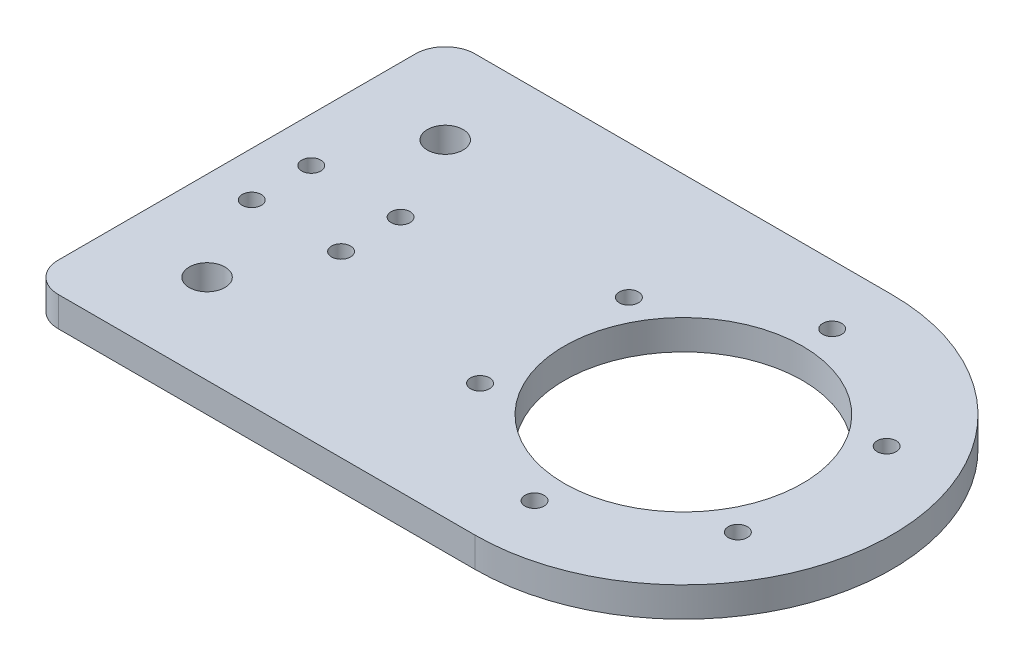
SolidWorks part; units mm, degrees
ref_plane "Front Plane" through (0, 0, 0) normal (0, 0, 1) x (1, 0, 0)
ref_plane "Top Plane" through (0, 0, 0) normal (0, 1, 0) x (1, 0, 0)
ref_plane "Right Plane" through (0, 0, 0) normal (1, 0, 0) x (0, 0, -1)
sketch "Sketch1" plane through (0, 0, 0) normal (0, 1, 0) x (1, 0, 0)
  line L0 (-75, 35) -> (0, 35)
  line L1 (0, -35) -> (-75, -35)
  line L2 (-75, -35) -> (-75, 35)
  line L3 (-60, 20) -> (-60, -20) construction
  line L4 (-103.0809, 0) -> (63.3859, 0) construction
  line L5 (-67.5, 5) -> (-52.5, 5) construction
  line L6 (-67.5, 5) -> (-67.5, -5) construction
  line L7 (-67.5, -5) -> (-52.5, -5) construction
  line L8 (-52.5, 5) -> (-52.5, -5) construction
  line L9 (-67.5, 5) -> (-52.5, -5) construction
  line L10 (-67.5, -5) -> (-52.5, 5) construction
  circle A0 centre (0, 0) radius 25 construction
  circle A1 centre (0, 25) radius 1.6
  arc A2 (0, 35) -> (0, -35) centre (0, 0) cw
  circle A3 centre (21.6506, 12.5) radius 1.6
  circle A4 centre (21.6506, -12.5) radius 1.6
  circle A5 centre (0, -25) radius 1.6
  circle A6 centre (-21.6506, -12.5) radius 1.6
  circle A7 centre (-21.6506, 12.5) radius 1.6
  circle A8 centre (0, 0) radius 20
  circle A11 centre (-67.5, 5) radius 1.6
  circle A12 centre (-52.5, 5) radius 1.6
  circle A13 centre (-52.5, -5) radius 1.6
  circle A14 centre (-67.5, -5) radius 1.6
  circle A15 centre (-60, 20) radius 3
  circle A16 centre (-60, -20) radius 3
  point P11 (-60, 0)
  point P23 (0, 0)
  dimension "D1" = 3.2
  dimension "D2" = 50
  dimension "D6" = 40
  dimension "D8" = 15
  dimension "D10" = 3.2
  dimension "D13" = 6
  dimension "D3" = 75
  dimension "D4" = 70
  dimension "D7" = 15
  dimension "D9" = 10
  dimension "D11" = 20
  dimension "D12" = 20
  dimension "D5" = 6
extrude "Boss-Extrude1" add sketch "Sketch1" along normal blind 5
fillet "Fillet1" radius 5 2 edges at (-75, 2.5, -35) (-75, 2.5, 35)
sketch "Sketch4" plane through (0, 0, 0) normal (0, -1, 0) x (1, 0, 0)
  circle A0 centre (0, 0) radius 25 construction
  circle A1 centre (0, 25) radius 3.25
  circle A2 centre (21.6506, 12.5) radius 3.25
  circle A3 centre (21.6506, -12.5) radius 3.25
  circle A4 centre (0, -25) radius 3.25
  circle A5 centre (-21.6506, -12.5) radius 3.25
  circle A6 centre (-21.6506, 12.5) radius 3.25
  point P18 (0, 0)
  dimension "D1" = 6.5
  dimension "D2" = 6
extrude "Cut-Extrude2" cut sketch "Sketch4" against normal blind 1.5
